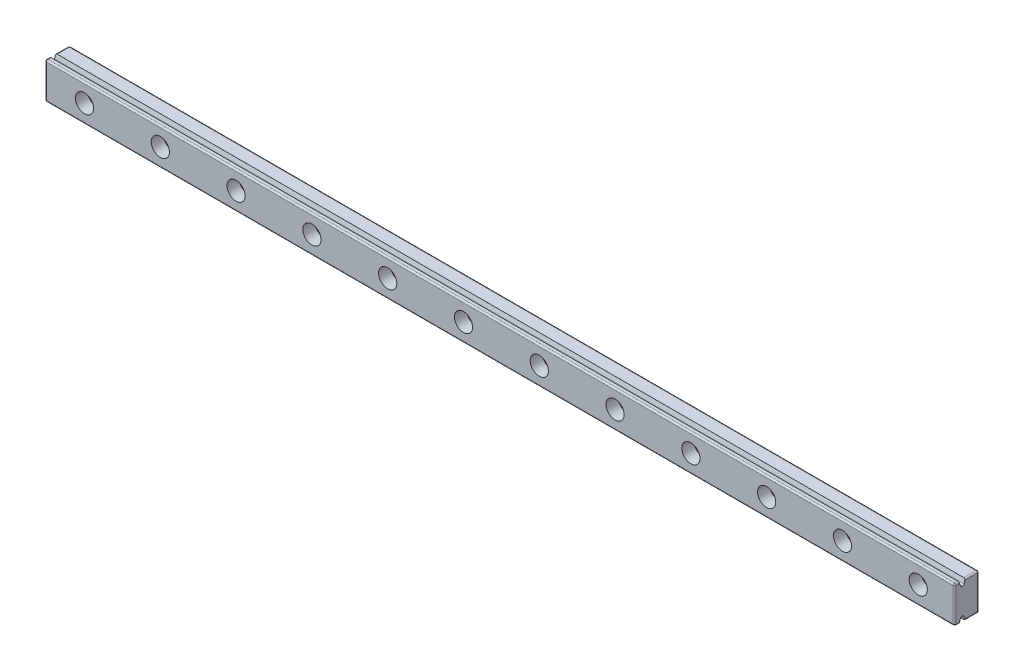
SolidWorks part; units mm, degrees
ref_plane "Front Plane" through (0, 0, 0) normal (0, 0, 1) x (1, 0, 0)
ref_plane "Top Plane" through (0, 0, 0) normal (0, 1, 0) x (1, 0, 0)
ref_plane "Right Plane" through (0, 0, 0) normal (1, 0, 0) x (0, 0, -1)
sketch "Sketch1" plane through (0, 0, 0) normal (1, 0, 0) x (0, 0, -1)
  line L0 (-0.5, 6) -> (4, 6)
  line L1 (-4, 6) -> (-2.5, 6)
  line L2 (-4, 6) -> (-4, -6)
  line L3 (-4, -6) -> (-2.5, -6)
  line L4 (4, 6) -> (4, -6)
  line L5 (-4, 6) -> (4, -6) construction
  line L6 (-4, -6) -> (4, 6) construction
  line L8 (-2.5, 6) -> (-2.5, 4.25)
  line L9 (-2.5, 4.25) -> (-0.5, 4.25)
  line L10 (-0.5, 6) -> (-0.5, 4.25)
  line L12 (-2.5, -6) -> (-2.5, -4.25)
  line L13 (-2.5, -4.25) -> (-0.5, -4.25)
  line L14 (-0.5, -6) -> (-0.5, -4.25)
  line L15 (-0.5, -6) -> (4, -6)
  point P0 (0, 0)
  dimension "D1" = 12
  dimension "D2" = 8
  dimension "D3" = 2
  dimension "D4" = 2
  dimension "D5" = 1.5
  dimension "D6" = 1.5
  dimension "D7" = 8.5
  dimension "D8" = 4.25
extrude "Boss-Extrude1" add sketch "Sketch1" along normal blind 300
sketch "Sketch2" plane through (0, 0, 4) normal (0, 0, 1) x (1, 0, 0)
  line L0 (0, 6) -> (0, -6) construction
  circle A0 centre (13, 0) radius 1.75
  circle A1 centre (38, 0) radius 1.75
  circle A2 centre (63, 0) radius 1.75
  circle A3 centre (88, 0) radius 1.75
  circle A4 centre (113, 0) radius 1.75
  circle A5 centre (138, 0) radius 1.75
  circle A6 centre (163, 0) radius 1.75
  circle A7 centre (188, 0) radius 1.75
  circle A8 centre (213, 0) radius 1.75
  circle A9 centre (238, 0) radius 1.75
  circle A10 centre (263, 0) radius 1.75
  circle A11 centre (288, 0) radius 1.75
  circle A12 centre (313, 0) radius 1.75
  circle A13 centre (338, 0) radius 1.75
  circle A14 centre (363, 0) radius 1.75
  circle A15 centre (388, 0) radius 1.75
  dimension "D1" = 3.5
  dimension "D2" = 13
  dimension "D3" = 16
extrude "Cut-Extrude1" cut sketch "Sketch2" against normal blind 10
sketch "Sketch3" plane through (0, 0, 4) normal (0, 0, 1) x (1, 0, 0)
  circle A0 centre (13, 0) radius 3
  circle A1 centre (38, 0) radius 3
  circle A2 centre (63, 0) radius 3
  circle A3 centre (88, 0) radius 3
  circle A4 centre (113, 0) radius 3
  circle A5 centre (138, 0) radius 3
  circle A6 centre (163, 0) radius 3
  circle A7 centre (188, 0) radius 3
  circle A8 centre (213, 0) radius 3
  circle A9 centre (238, 0) radius 3
  circle A10 centre (263, 0) radius 3
  circle A11 centre (288, 0) radius 3
  circle A12 centre (313, 0) radius 3
  circle A13 centre (338, 0) radius 3
  circle A14 centre (363, 0) radius 3
  circle A15 centre (388, 0) radius 3
  dimension "D1" = 6
  dimension "D2" = 16
extrude "Cut-Extrude2" cut sketch "Sketch3" against normal blind 4
chamfer "Chamfer1" distance 0.5 angle 74 4 edges at (150, -4.25, 2.5) (150, -4.25, 0.5) (150, 4.25, 2.5) (150, 4.25, 0.5)
fillet "Fillet1" radius 0.5 20 edges at (300, -6, -1.75) (300, 0, -4) (300, 6, -1.75) (300, 6, 3.25) (300, 0, 4) (300, -6, 3.25) (0, -6, 3.25) (0, -6, -1.75) (0, 0, -4) (0, 6, -1.75) (0, 6, 3.25) (0, 0, 4) (150, -4.25, 1) (150, -4.25, 2) (150, 4.25, 2) (150, 4.25, 1) (150, -6, 4) (150, 6, 4) (150, -6, -4) (150, 6, -4)
